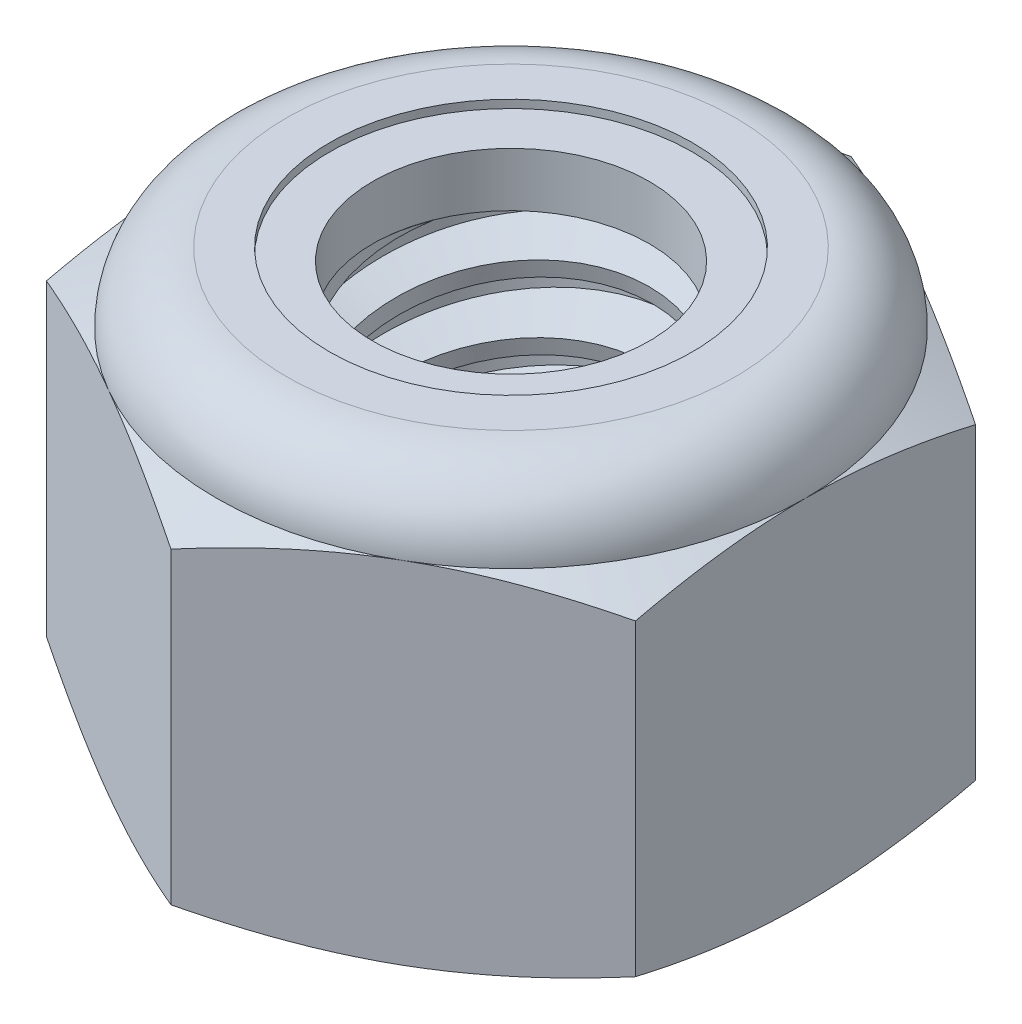
SolidWorks part; units mm, degrees
material "Cast Alloy Steel"
ref_plane "Front" through (0, 0, 0) normal (0, 0, 1) x (1, 0, 0)
ref_plane "Top" through (0, 0, 0) normal (0, 1, 0) x (1, 0, 0)
ref_plane "Right" through (0, 0, 0) normal (1, 0, 0) x (0, 0, -1)
sketch "Sketch1" plane through (0, 0, 0) normal (0, 1, 0) x (1, 0, 0)
  line L1 (0, 6.4158) -> (-5.5563, 3.2079)
  line L2 (-5.5563, 3.2079) -> (-5.5563, -3.2079)
  line L3 (-5.5563, -3.2079) -> (0, -6.4158)
  line L4 (0, -6.4158) -> (5.5562, -3.2079)
  line L5 (5.5562, -3.2079) -> (5.5562, 3.2079)
  line L6 (5.5562, 3.2079) -> (0, 6.4158)
  circle A0 centre (0, 0) radius 5.5563 construction
  dimension "Hex Flats" = 11.1125
extrude "Extrude1" add sketch "Sketch1" along normal blind 7.9375
sketch "Sketch2" plane through (0, 0, 0) normal (1, 0, 0) x (0, 0, -1)
  line L0 (-3.175, 0) -> (-3.175, 7.9375) construction
  line L1 (0, 0) -> (3.175, 0)
  line L2 (0, 0) -> (0, 7.9375)
  line L3 (0, 7.9375) -> (3.175, 7.9375)
  line L4 (3.175, 0) -> (3.175, 7.9375)
  line L5 (-3.2079, 7.9375) -> (3.2079, 7.9375) construction
  line L7 (0, -3.175) -> (0, 0) construction
  dimension "Thread Dia" = 6.35
revolve "Revolve1" add sketch "Sketch2" angle 360 about L7
sketch "Sketch3" plane through (0, 0, 0) normal (1, 0, 0) x (0, 0, -1)
  line L0 (3.175, 7.9375) -> (-3.175, 7.9375) construction
  line L1 (-3.175, 7.9375) -> (-3.175, 6.6675) construction
  line L2 (-3.175, 6.6675) -> (3.175, 7.9375) construction
  line L3 (3.175, 7.9375) -> (3.2061, 7.7818) construction
  line L4 (3.2061, 7.7818) -> (3.4241, 6.6922)
  line L5 (3.4241, 6.6922) -> (2.6722, 6.9465)
  line L6 (2.6722, 6.9465) -> (2.6099, 7.2579)
  line L7 (2.6099, 7.2579) -> (3.2061, 7.7818)
  line L8 (2.641, 7.1022) -> (3.3151, 7.237) construction
  line L9 (3.175, 7.9375) -> (3.175, 7.209) construction
  line L10 (3.175, 7.209) -> (-3.175, 5.939) construction
  line L11 (-3.175, 5.939) -> (-3.175, 6.6675) construction
  line L12 (-0.2727, 7.9375) -> (0.2727, 5.2105) construction
  line L13 (-3.175, 0) -> (-3.175, 7.9375) construction
  line L14 (0, 7.9375) -> (3.175, 7.9375) construction
  line L15 (3.175, 0) -> (3.175, 7.9375) construction
  point P13 (0, 6.574)
  dimension "D1" = 0.1588
  dimension "D2" = 0.3175
  dimension "Thread Pitch" = 1.27
  dimension "D4" = 60
  dimension "D5" = 1.27
revolve "Cut-Revolve1" cut sketch "Sketch3" angle 360 about L12
pattern_linear "LPattern1" count 6 spacing 1.27 along (0, -1, 0) count 2 spacing 1.27 along (0, 1, 0) of "Cut-Revolve1"
sketch "Sketch4" plane through (0, 0, 0) normal (1, 0, 0) x (0, 0, -1)
  line L0 (0, 7.9375) -> (3.175, 7.9375)
  line L1 (3.175, 7.9375) -> (2.6099, 7.674)
  line L2 (2.6099, 7.674) -> (2.6099, 0.2635)
  line L3 (2.6099, 0.2635) -> (3.175, 0)
  line L4 (3.175, 0) -> (0, 0)
  line L5 (0, 0) -> (0, 7.9375)
  line L6 (3.175, 0) -> (3.175, 7.9375) construction
  line L7 (0, 7.9375) -> (3.175, 7.9375) construction
  line L8 (0, 0) -> (3.175, 0) construction
  line L9 (0, 0) -> (0, 7.9375) construction
  line L10 (0, 7.9375) -> (0, 8.561) construction
  dimension "D1" = 25
revolve "Cut-Revolve2" cut sketch "Sketch4" angle 360 about L10
combine bodies "Combine1" operation type subtract main body 112 bodies to subtract 111
sketch "Sketch5" plane through (0, 0, 0) normal (1, 0, 0) x (0, 0, -1)
  line L0 (0, 0) -> (5.5563, 0)
  line L1 (5.5563, 0) -> (6.4158, 0.4008)
  line L2 (6.4158, 0.4008) -> (6.4158, 6.2138)
  line L3 (6.4158, 6.2138) -> (5.5563, 6.6146)
  line L4 (4.2333, 7.9375) -> (4.2333, 9.2075)
  line L5 (4.2333, 9.2075) -> (7.6858, 9.2075)
  line L6 (7.6858, 9.2075) -> (7.6858, -1.27)
  line L7 (7.6858, -1.27) -> (0, -1.27)
  line L8 (0, -1.27) -> (0, 0)
  line L9 (5.5563, 6.6146) -> (5.5563, 0) construction
  line L10 (0, 0) -> (3.175, 0) construction
  line L13 (6.4158, 3.3073) -> (7.6858, 3.3073) construction
  line L14 (6.4158, 7.9375) -> (6.4158, 0) construction
  line L15 (0, 0) -> (0, 9.2075) construction
  line L20 (0, 9.2075) -> (4.2333, 9.2075) construction
  line L22 (0, 7.9375) -> (3.175, 7.9375) construction
  arc A0 (5.5563, 6.6146) -> (4.2333, 7.9375) centre (4.2333, 6.6146) ccw
  dimension "D1" = 25
  dimension "D2" = 1.27
  dimension "D3" = 7.9375
  dimension "D4" = 1.3229
revolve "Cut-Revolve3" cut sketch "Sketch5" angle 360 about L15
sketch "Sketch6" plane through (0, 0, 0) normal (1, 0, 0) x (0, 0, -1)
  line L0 (0, 6.6146) -> (5.4039, 6.6146)
  line L1 (4.2333, 7.7851) -> (3.4216, 7.7851)
  line L2 (0, 9.2075) -> (0, 6.6146)
  line L3 (3.4216, 9.2075) -> (0, 9.2075)
  line L4 (0, 9.2075) -> (4.2333, 9.2075) construction
  line L5 (0, 0) -> (0, 9.2075) construction
  line L6 (0, 9.2075) -> (0, 44.323) construction
  line L7 (3.4216, 7.7851) -> (3.4216, 9.2075)
  line L8 (4.2333, 7.9375) -> (4.2333, 7.7851) construction
  line L9 (3.4216, 7.7851) -> (2.6099, 7.7851) construction
  line L10 (2.6099, 7.7851) -> (2.6099, 7.674) construction
  arc A0 (5.4039, 6.6146) -> (4.2333, 7.7851) centre (4.2333, 6.6146) ccw
  arc A1 (5.5563, 6.6146) -> (4.2333, 7.9375) centre (4.2333, 6.6146) ccw construction
  dimension "D1" = 0.1524
revolve "Cut-Revolve4" cut sketch "Sketch6" angle 360 about L6
sketch "Sketch7" plane through (0, 0, 0) normal (1, 0, 0) x (0, 0, -1)
  line L0 (2.6099, 6.6908) -> (5.325, 6.6908)
  line L1 (4.2333, 7.7089) -> (2.6099, 7.7089)
  line L2 (2.6099, 7.7089) -> (2.6099, 6.6908)
  line L3 (2.6099, 6.6908) -> (0, 6.6908) construction
  line L4 (0, 6.6908) -> (0, 7.7089) construction
  line L5 (0, 7.7089) -> (2.6099, 7.7089) construction
  line L6 (2.6099, 6.6908) -> (2.6099, 6.6146) construction
  line L7 (0, 6.6146) -> (5.4039, 6.6146) construction
  line L8 (4.2333, 7.7089) -> (4.2333, 7.7851) construction
  arc A0 (5.325, 6.6908) -> (4.2333, 7.7089) centre (4.2333, 6.6146) ccw
  arc A2 (5.4039, 6.6146) -> (4.2333, 7.7851) centre (4.2333, 6.6146) ccw construction
  dimension "D1" = 0.0762
revolve "Revolve2" add sketch "Sketch7" angle 360 about L4
equation "\"D1@Sketch3\"=\"Thread Pitch@Sketch3\"/8"
equation "\"D2@Sketch3\"=\"Thread Pitch@Sketch3\"/4"
equation "\"D5@Sketch3\"=\"Thread Pitch@Sketch3\""
equation "\"D4@LPattern1\"=\"Thread Pitch@Sketch3\""
equation "\"D3@LPattern1\"=\"Thread Pitch@Sketch3\""
equation "\"D1@LPattern1\"=\"Height@Extrude1\"/\"Thread Pitch@Sketch3\""
equation "\"D4@Sketch5\"=\"Height@Extrude1\"/6"
